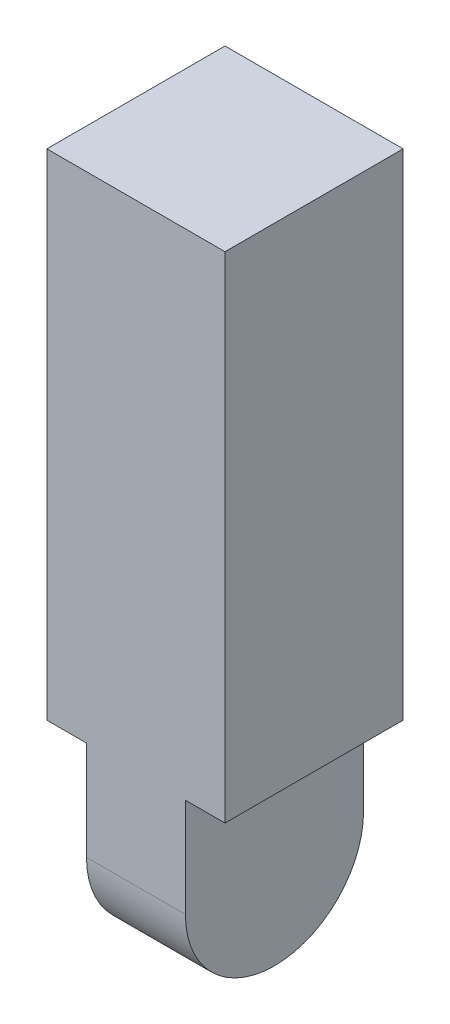
SolidWorks part; units mm, degrees
ref_plane "Front" through (0, 0, 0) normal (0, 0, 1) x (1, 0, 0)
ref_plane "Top" through (0, 0, 0) normal (0, 1, 0) x (1, 0, 0)
ref_plane "Right" through (0, 0, 0) normal (1, 0, 0) x (0, 0, -1)
sketch "草图1" plane through (0, 0, 0) normal (0, 1, 0) x (1, 0, 0)
  line L1 (-9, 9) -> (9, 9)
  line L2 (-9, 9) -> (-9, -9)
  line L3 (-9, -9) -> (9, -9)
  line L4 (9, 9) -> (9, -9)
  dimension "D1" = 18
  dimension "D2" = 18
  dimension "D3" = 9
  dimension "D4" = 9
extrude "凸台-拉伸1" add sketch "草图1" along normal blind 50
sketch "草图2" plane through (0, 0, 0) normal (1, 0, 0) x (0, 0, -1)
  line L5 (-9, -10) -> (-9, 1.0378)
  line L6 (-9, 1.0378) -> (9, 1.0378)
  line L7 (9, -10) -> (9, 1.0378)
  arc A1 (-9, -10) -> (9, -10) centre (0, -10) ccw
extrude "凸台-拉伸2" add sketch "草图2" along normal mid plane 10
